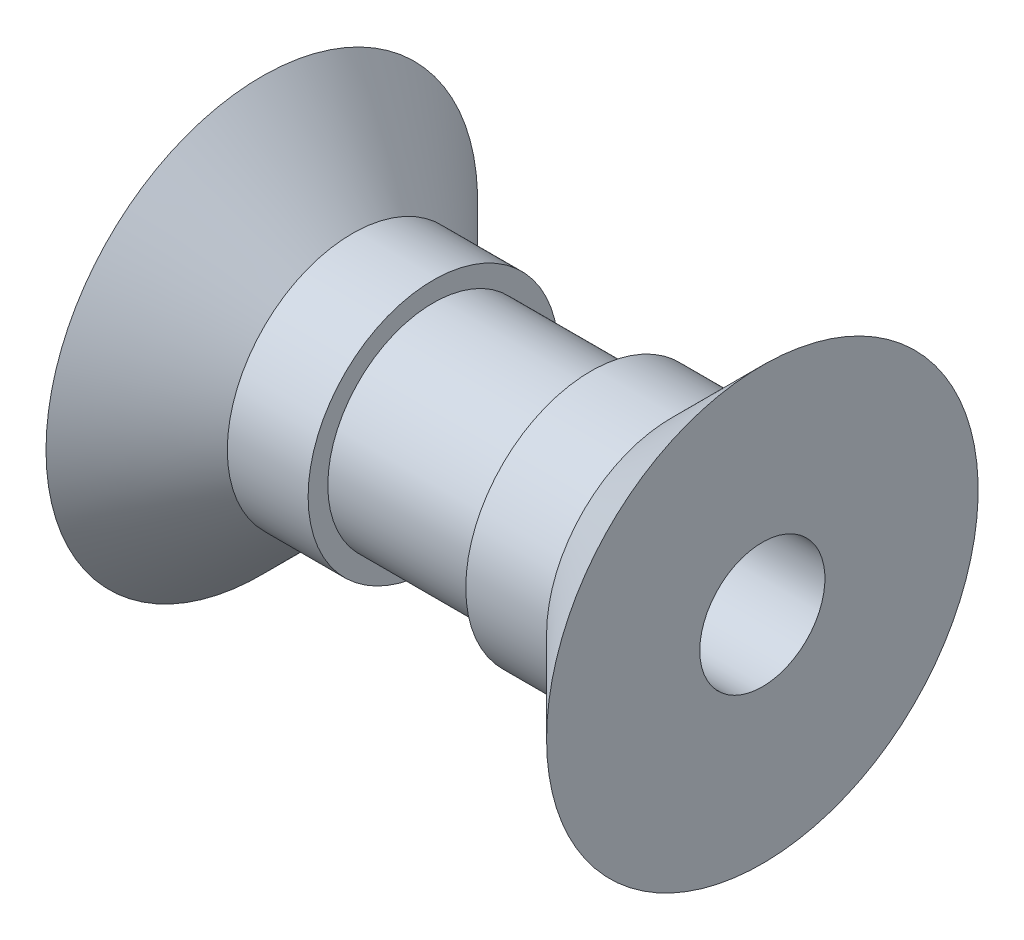
SolidWorks part; units mm, degrees
ref_plane "Front Plane" through (0, 0, 0) normal (0, 0, 1) x (1, 0, 0)
ref_plane "Top Plane" through (0, 0, 0) normal (0, 1, 0) x (1, 0, 0)
ref_plane "Right Plane" through (0, 0, 0) normal (1, 0, 0) x (0, 0, -1)
sketch "Sketch1" plane through (0, 0, 0) normal (0, 0, 1) x (1, 0, 0)
  line L0 (-93.9518, 0) -> (103.338, 0) construction
  line L1 (-6.35, 0) -> (-6.35, 5.475)
  line L2 (-6.35, 5.475) -> (-4.05, 3.175)
  line L3 (-4.05, 3.175) -> (-2, 3.175)
  line L4 (-2, 3.175) -> (-2, 2.675)
  line L5 (-2, 2.675) -> (2, 2.675)
  line L6 (0, -10.0179) -> (0, 20.3066) construction
  line L7 (93.9518, 0) -> (-103.338, 0) construction
  line L8 (2, 3.175) -> (2, 2.675)
  line L9 (4.05, 3.175) -> (2, 3.175)
  line L10 (6.35, 5.475) -> (4.05, 3.175)
  line L11 (6.35, 0) -> (6.35, 5.475)
  line L12 (-6.35, 0) -> (6.35, 0)
  point P14 (0, 2.675)
  dimension "D1" = 6.35
  dimension "D2" = 4
  dimension "D3" = 8.1
  dimension "D4" = 0.5
  dimension "D5" = 135
  dimension "D6" = 3.175
revolve "Revolve1" add sketch "Sketch1" angle 360 about L0
sketch "Sketch2" plane through (-6.35, 0, 0) normal (-1, 0, 0) x (0, 0, 1)
  circle A0 centre (0, 0) radius 1.5875
  dimension "D1" = 3.175
extrude "Cut-Extrude1" cut sketch "Sketch2" against normal through all
sketch "Sketch3" plane through (6.35, 0, 0) normal (1, 0, 0) x (0, 0, -1)
  circle A0 centre (0, 0) radius 17.4353
extrude "Cut-Extrude2" [suppressed] cut sketch "Sketch3" against normal up to vertex
sketch "Sketch4" [suppressed] plane through (0, 0, 0) normal (1, 0, 0) x (0, 0, -1)
  line L0 (0, 3.9269) -> (0, -4.4745) construction
  line L1 (-4.3015, 0) -> (4.5177, 0) construction
